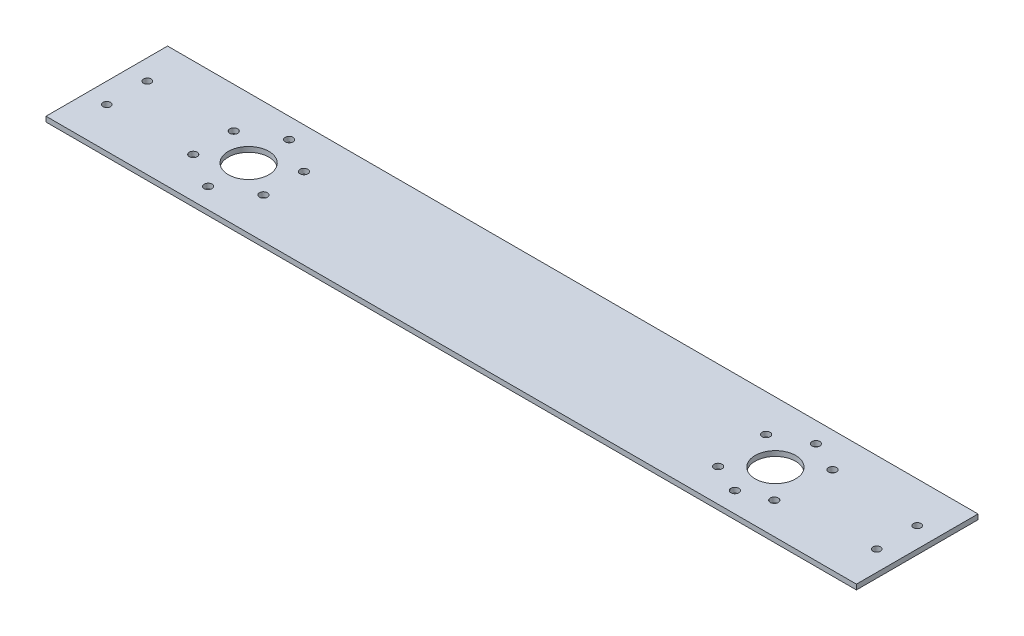
SolidWorks part; units mm, degrees
material "6061 Alloy"
ref_plane "Front Plane" through (0, 0, 0) normal (0, 0, 1) x (1, 0, 0)
ref_plane "Top Plane" through (0, 0, 0) normal (0, 1, 0) x (1, 0, 0)
ref_plane "Right Plane" through (0, 0, 0) normal (1, 0, 0) x (0, 0, -1)
sketch "Sketch1" plane through (0, 0, 0) normal (0, 1, 0) x (1, 0, 0)
  line L1 (254, -38.1) -> (-254, -38.1)
  line L2 (254, -38.1) -> (254, 38.1)
  line L3 (254, 38.1) -> (-254, 38.1)
  line L4 (-254, -38.1) -> (-254, 38.1)
  line L5 (254, -38.1) -> (-254, 38.1) construction
  line L6 (254, 38.1) -> (-254, -38.1) construction
  point P0 (0, 0)
  dimension "D1" = 508
  dimension "D2" = 76.2
extrude "Boss-Extrude1" add sketch "Sketch1" along normal blind 3.175
sketch "Sketch3" plane through (0, 3.175, 0) normal (0, 1, 0) x (1, 0, 0)
  line L1 (-241.3, 38.1) -> (-241.3, 12.7) construction
  line L2 (254, 38.1) -> (-254, 38.1) construction
  line L3 (-241.3, 12.7) -> (-241.3, -12.7) construction
  line L4 (-241.3, -12.7) -> (-241.3, -38.1) construction
  line L5 (-254, -38.1) -> (254, -38.1) construction
  line L6 (-254, 38.1) -> (-254, -38.1) construction
  line L7 (-254, 38.1) -> (254, 38.1) construction
  line L8 (0, 38.1) -> (0, -38.1) construction
  line L9 (241.3, -12.7) -> (241.3, -38.1) construction
  line L10 (241.3, 12.7) -> (241.3, -12.7) construction
  line L11 (241.3, 38.1) -> (241.3, 12.7) construction
  circle A0 centre (-241.3, 12.7) radius 2.3813
  circle A1 centre (-241.3, -12.7) radius 2.3813
  circle A2 centre (241.3, -12.7) radius 2.3813
  circle A3 centre (241.3, 12.7) radius 2.3813
  dimension "D2" = 25.4
  dimension "D3" = 4.7625
  dimension "D1" = 12.7
extrude "Cut-Extrude2" cut sketch "Sketch3" against normal blind 3.175
sketch "Sketch4" plane through (0, 3.175, 0) normal (0, 1, 0) x (1, 0, 0)
  line L0 (-254, 0) -> (-165.1, 0) construction
  line L1 (-254, 38.1) -> (-254, -38.1) construction
  line L2 (0, 38.1) -> (0, -38.1) construction
  line L3 (254, 38.1) -> (-254, 38.1) construction
  line L4 (-254, -38.1) -> (254, -38.1) construction
  line L5 (254, 0) -> (165.1, 0) construction
  circle A0 centre (-165.1, 0) radius 12.7
  circle A1 centre (165.1, 0) radius 12.7
  dimension "D1" = 25.4
  dimension "D2" = 88.9
extrude "Cut-Extrude3" cut sketch "Sketch4" against normal through all both
sketch "Sketch5" plane through (0, 3.175, 0) normal (0, 1, 0) x (1, 0, 0)
  line L0 (-187.097, 12.7) -> (-187.097, -12.7) construction
  line L1 (-187.097, -12.7) -> (-165.1, -25.4) construction
  line L2 (-165.1, -25.4) -> (-143.103, -12.7) construction
  line L3 (-143.103, -12.7) -> (-143.103, 12.7) construction
  line L4 (-143.103, 12.7) -> (-165.1, 25.4) construction
  line L5 (-165.1, 25.4) -> (-187.097, 12.7) construction
  circle A0 centre (-165.1, 0) radius 25.4 construction
  circle A1 centre (165.1, 0) radius 25.4 construction
  circle A2 centre (165.1, 25.4) radius 2.4892
  circle A3 centre (165.1, -25.4) radius 2.4892
  circle A4 centre (182.7023, -18.3117) radius 2.4892
  circle A5 centre (146.7812, -17.595) radius 2.4892
  circle A6 centre (144.4784, 14.8293) radius 2.4892
  circle A7 centre (184.4284, 16.4794) radius 2.4892
  circle A8 centre (-165.1, 25.4) radius 2.4892
  circle A9 centre (-165.1, -25.4) radius 2.4892
  circle A10 centre (-143.103, -12.7) radius 2.4892
  circle A11 centre (-143.103, 12.7) radius 2.4892
  circle A12 centre (-187.097, 12.7) radius 2.4892
  circle A13 centre (-187.097, -12.7) radius 2.4892
  dimension "D1" = 4.9784
  dimension "D2" = 50.8
  dimension "D3" = 50.8
extrude "Cut-Extrude4" cut sketch "Sketch5" against normal through all both and the other way through all
